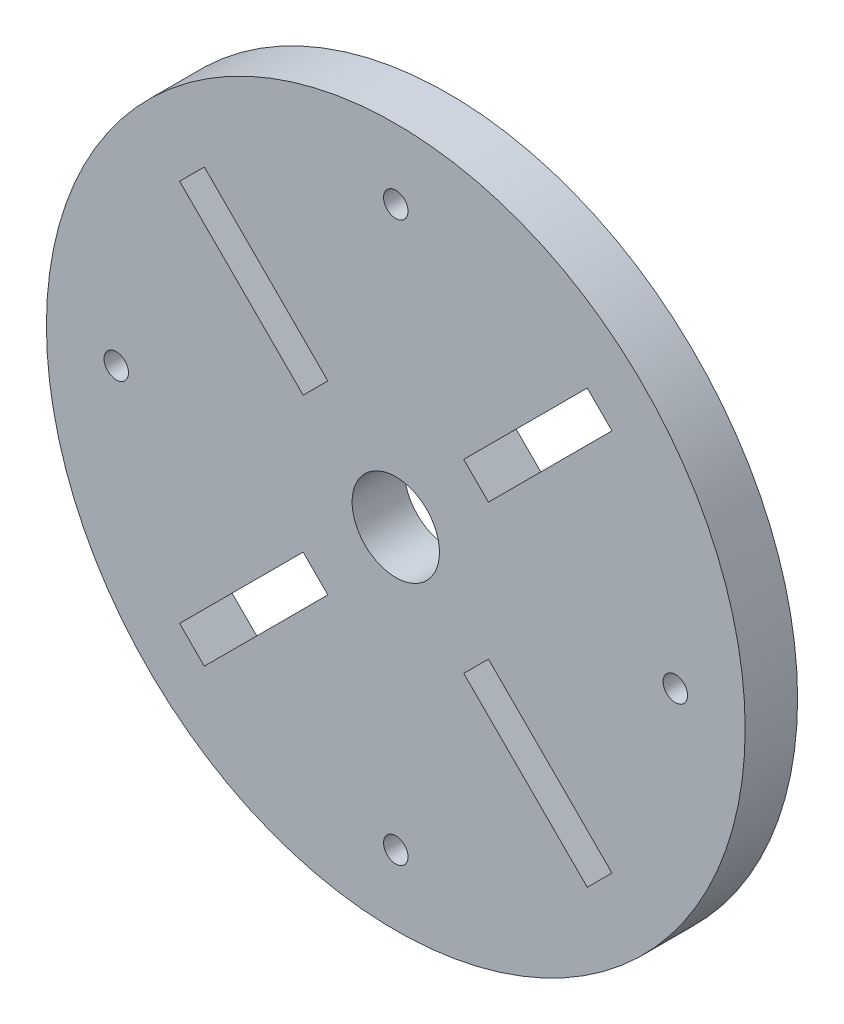
SolidWorks part; units mm, degrees
material "ﾊﾞﾙｻ"
ref_plane "正面" through (0, 0, 0) normal (0, 0, 1) x (1, 0, 0)
ref_plane "平面" through (0, 0, 0) normal (0, 1, 0) x (1, 0, 0)
ref_plane "右側面" through (0, 0, 0) normal (1, 0, 0) x (0, 0, -1)
sketch "ｽｹｯﾁ1" plane through (0, 0, 0) normal (0, 0, 1) x (1, 0, 0)
  line L0 (0, 0) -> (0, 27.1367) construction
  circle A0 centre (0, 0) radius 20
  dimension "D3" = 40
extrude "ﾎﾞｽ - 押し出し1" add sketch "ｽｹｯﾁ1" along normal blind 3
sketch "ｽｹｯﾁ2" plane through (0, 0, 3) normal (0, 0, 1) x (1, 0, 0)
  line L0 (0, 0) -> (0, 20.2138) construction
  circle A0 centre (0, 16) radius 0.7
  circle A1 centre (0, 0) radius 20 construction
  dimension "D1" = 1.4
  dimension "D2" = 16
extrude "ｶｯﾄ - 押し出し1" cut sketch "ｽｹｯﾁ2" against normal up to next (3 mm away)
pattern_circular "円形ﾊﾟﾀｰﾝ2" count 4 over 360 about axis through (0, 0, 0) along (0, 0, 1) of "ｶｯﾄ - 押し出し1"
sketch "ｽｹｯﾁ3" plane through (0, 0, 3) normal (0, 0, 1) x (1, 0, 0)
  line L0 (0, 0) -> (0, 5.4677) construction
  line L1 (0, 0) -> (13.9108, 13.9108) construction
  line L2 (11.3137, 7.7782) -> (7.7782, 11.3137)
  line L3 (7.7782, 11.3137) -> (4.9497, 8.4853)
  line L4 (4.9497, 8.4853) -> (8.4853, 4.9497)
  line L5 (0, 0) -> (5.4677, 0) construction
  line L6 (11.3137, 7.7782) -> (8.4853, 4.9497)
  point P10 (6.7175, 6.7175)
  point P11 (9.5459, 9.5459)
  dimension "D1" = 45
  dimension "D2" = 4
  dimension "D3" = 2.5
  dimension "D4" = 9.5
extrude "ｶｯﾄ - 押し出し2" [suppressed] cut sketch "ｽｹｯﾁ3" against normal up to next
pattern_circular "円形ﾊﾟﾀｰﾝ3" [suppressed] count 4 over 360
sketch "ｽｹｯﾁ4" plane through (0, 0, 3) normal (0, 0, 1) x (1, 0, 0)
  circle A0 centre (0, 0) radius 2.5
  dimension "D1" = 5
extrude "ｶｯﾄ - 押し出し3" cut sketch "ｽｹｯﾁ4" against normal blind 3
sketch "ｽｹｯﾁ5" plane through (0, 0, 3) normal (0, 0, 1) x (1, 0, 0)
  line L0 (0, 0) -> (4.5962, 4.5962) construction
  line L1 (4.5962, 4.5962) -> (3.8891, 5.3033)
  line L2 (3.8891, 5.3033) -> (10.9602, 12.3744)
  line L3 (10.9602, 12.3744) -> (12.3744, 10.9602)
  line L4 (12.3744, 10.9602) -> (5.3033, 3.8891)
  line L5 (5.3033, 3.8891) -> (4.5962, 4.5962)
  line L6 (0, 0) -> (9.4049, 0) construction
  circle A0 centre (0, 0) radius 2 construction
  point P10 (12.3777, 10.9568)
  dimension "D1" = 6.5
  dimension "D2" = 45
  dimension "D3" = 2
  dimension "D4" = 10
extrude "ｶｯﾄ - 押し出し4" cut sketch "ｽｹｯﾁ5" against normal up to next (3 mm away)
pattern_circular "円形ﾊﾟﾀｰﾝ4" count 4 over 360 about axis through (0, 0, 0) along (0, 0, 1) of "ｶｯﾄ - 押し出し4"
